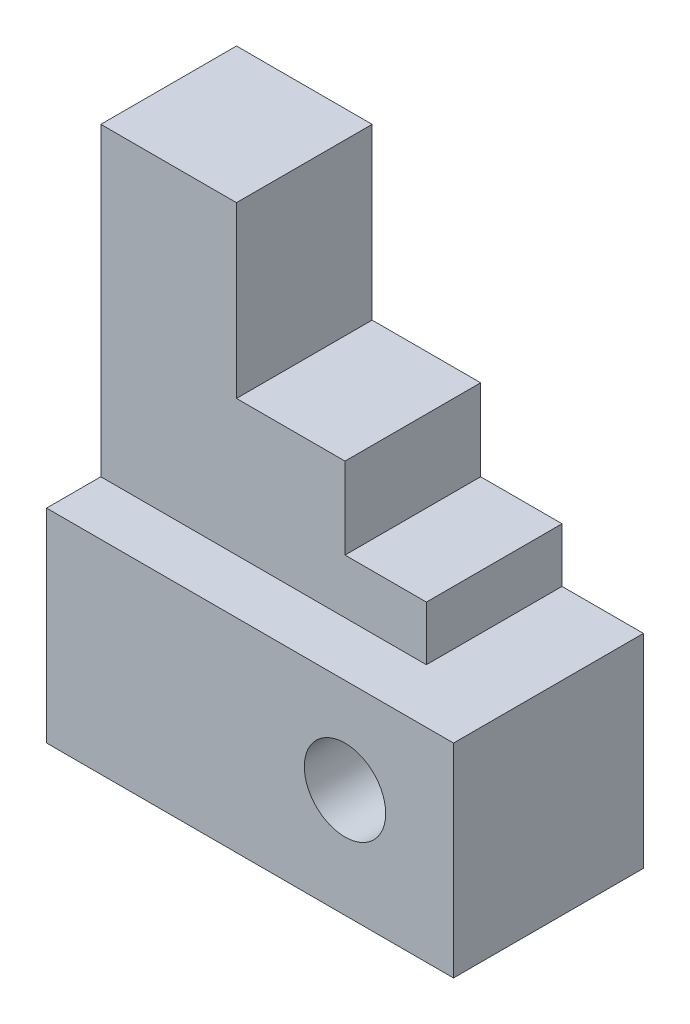
SolidWorks part; units mm, degrees
ref_plane "Front Plane" through (0, 0, 0) normal (0, 0, 1) x (1, 0, 0)
ref_plane "Top Plane" through (0, 0, 0) normal (0, 1, 0) x (1, 0, 0)
ref_plane "Right Plane" through (0, 0, 0) normal (1, 0, 0) x (0, 0, -1)
sketch "Sketch2" plane through (0, 0, 0) normal (0, 1, 0) x (1, 0, 0)
  line L1 (-30, 14) -> (30, 14)
  line L2 (-30, 14) -> (-30, -14)
  line L3 (-30, -14) -> (30, -14)
  line L4 (30, 14) -> (30, -14)
  line L5 (-30, 14) -> (30, -14) construction
  line L6 (-30, -14) -> (30, 14) construction
  point P0 (0, 0)
  dimension "D1" = 60
  dimension "D2" = 28
extrude "Boss-Extrude1" add sketch "Sketch2" along normal blind 30
sketch "Sketch3" plane through (0, 0, 14) normal (0, 0, 1) x (1, 0, 0)
  line L0 (30, 0) -> (14, 0) construction
  line L1 (-30, 0) -> (30, 0) construction
  line L2 (14, 0) -> (14, 16) construction
  circle A0 centre (14, 16) radius 6
  dimension "D1" = 16
  dimension "D2" = 16
extrude "Cut-Extrude1" cut sketch "Sketch3" against normal blind 47
sketch "Sketch4" plane through (0, 30, 0) normal (0, 1, 0) x (1, 0, 0)
  line L1 (-30, 14) -> (18, 14)
  line L2 (-30, 14) -> (-30, -6)
  line L3 (-30, -6) -> (18, -6)
  line L4 (18, 14) -> (18, -6)
  dimension "D1" = 48
  dimension "D2" = 20
extrude "Boss-Extrude2" add sketch "Sketch4" along normal blind 8
sketch "Sketch5" plane through (0, 38, 0) normal (0, 1, 0) x (1, 0, 0)
  line L0 (-30, -6) -> (18, -6) construction
  line L1 (-30, 14) -> (6, 14)
  line L2 (-30, 14) -> (-30, -6)
  line L3 (-30, -6) -> (6, -6)
  line L4 (6, 14) -> (6, -6)
  dimension "D1" = 36
extrude "Boss-Extrude3" add sketch "Sketch5" along normal blind 12
sketch "Sketch6" plane through (0, 50, 0) normal (0, 1, 0) x (1, 0, 0)
  line L0 (-30, -6) -> (6, -6) construction
  line L1 (-30, 14) -> (-10, 14)
  line L2 (-30, 14) -> (-30, -6)
  line L3 (-30, -6) -> (-10, -6)
  line L4 (-10, 14) -> (-10, -6)
  dimension "D1" = 20
extrude "Boss-Extrude4" add sketch "Sketch6" along normal blind 25
